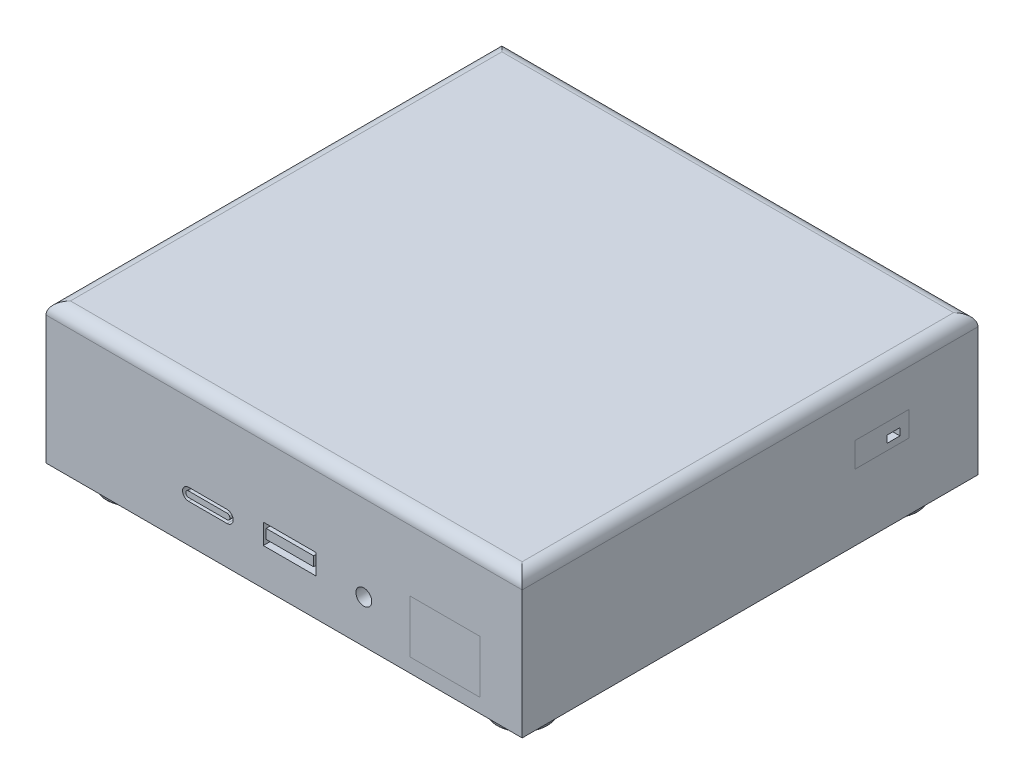
SolidWorks part; units mm, degrees
ref_plane "前视基准面" through (0, 0, 0) normal (0, 0, 1) x (1, 0, 0)
ref_plane "上视基准面" through (0, 0, 0) normal (0, 1, 0) x (1, 0, 0)
ref_plane "右视基准面" through (0, 0, 0) normal (1, 0, 0) x (0, 0, -1)
sketch "草图2" plane through (0, 0, 0) normal (0, 1, 0) x (1, 0, 0)
  line L1 (-58.5, -56) -> (58.5, -56)
  line L2 (-58.5, -56) -> (-58.5, 56)
  line L3 (-58.5, 56) -> (58.5, 56)
  line L4 (58.5, -56) -> (58.5, 56)
  line L5 (-58.5, -56) -> (58.5, 56) construction
  line L6 (-58.5, 56) -> (58.5, -56) construction
  point P0 (0, 0)
  dimension "D1" = 112
  dimension "D2" = 117
extrude "凸台-拉伸1" add sketch "草图2" along normal blind 34.5
fillet "圆角1" radius 3 4 edges at (0, 34.5, 56) (-58.5, 34.5, 0) (0, 34.5, -56) (58.5, 34.5, 0)
sketch "草图4" plane through (0, 0, 56) normal (0, 0, 1) x (1, 0, 0)
  line L1 (30.8918, 16.4329) -> (48.1943, 16.4329)
  line L2 (30.8918, 16.4329) -> (30.8918, 3.4592)
  line L3 (30.8918, 3.4592) -> (48.1943, 3.4592)
  line L4 (48.1943, 16.4329) -> (48.1943, 3.4592)
split line "分割线1"
sketch "草图5" plane through (0, 0, 56) normal (0, 0, 1) x (1, 0, 0)
  line L0 (-23.4533, 10.8763) -> (-14.0134, 10.8763) construction
  line L1 (-5.1124, 14.1395) -> (7.8876, 14.1395)
  line L2 (-5.1124, 14.1395) -> (-5.1124, 9.1395)
  line L3 (-5.1124, 9.1395) -> (7.8876, 9.1395)
  line L4 (7.8876, 14.1395) -> (7.8876, 9.1395)
  line L5 (-4.4095, 13.1395) -> (7.2461, 13.1395)
  line L6 (-4.4095, 13.1395) -> (-4.4095, 10.8025)
  line L7 (-4.4095, 10.8025) -> (7.2461, 10.8025)
  line L8 (7.2461, 13.1395) -> (7.2461, 10.8025)
  line L9 (-23.4533, 12.3763) -> (-14.0134, 12.3763)
  line L10 (-23.4533, 9.3763) -> (-14.0134, 9.3763)
  line L11 (-23.4533, 10.8763) -> (-14.0134, 10.8763) construction
  line L12 (-23.4533, 11.5763) -> (-14.0134, 11.5763)
  line L13 (-23.4533, 10.1763) -> (-14.0134, 10.1763)
  circle A0 centre (19.5946, 10.5373) radius 1.9432
  arc A1 (-23.4533, 12.3763) -> (-23.4533, 9.3763) centre (-23.4533, 10.8763) ccw
  arc A2 (-14.0134, 9.3763) -> (-14.0134, 12.3763) centre (-14.0134, 10.8763) ccw
  arc A3 (-23.4533, 11.5763) -> (-23.4533, 10.1763) centre (-23.4533, 10.8763) ccw
  arc A4 (-14.0134, 10.1763) -> (-14.0134, 11.5763) centre (-14.0134, 10.8763) ccw
  point P12 (-18.7333, 10.8763)
  point P17 (-18.7333, 10.8763)
  dimension "D1" = 13
  dimension "D2" = 5
  dimension "D3" = 1
  dimension "D4" = 0.703
  dimension "D5" = 1.4
  dimension "D6" = 3
extrude "切除-拉伸1" cut sketch "草图5" against normal blind 34.5
sketch "草图6" plane through (58.5, 0, 0) normal (1, 0, 0) x (0, 0, -1)
  line L1 (25.7543, 22.4016) -> (38.9963, 22.4016)
  line L2 (25.7543, 22.4016) -> (25.7543, 16.3039)
  line L3 (25.7543, 16.3039) -> (38.9963, 16.3039)
  line L4 (38.9963, 22.4016) -> (38.9963, 16.3039)
split line "分割线2"
sketch "草图7" plane through (58.5, 0, 0) normal (1, 0, 0) x (0, 0, -1)
  line L1 (33.6904, 19.6204) -> (36.8117, 19.6204)
  line L2 (33.6904, 19.6204) -> (33.6904, 17.871)
  line L3 (33.6904, 17.871) -> (36.8117, 17.871)
  line L4 (36.8117, 19.6204) -> (36.8117, 17.871)
extrude "切除-拉伸2" cut sketch "草图7" against normal blind 34.5
sketch "草图9" plane through (0, 0, -56) normal (0, 0, -1) x (-1, 0, 0)
  line L0 (-37.9278, 26.9668) -> (-37.9278, 21.2789)
  line L1 (-42.9278, 27.9668) -> (-41.2237, 27.9668)
  line L2 (-43.9278, 26.9668) -> (-43.9278, 21.2789)
  line L3 (-42.9278, 20.2789) -> (-41.2237, 20.2789)
  line L4 (-40.2237, 26.9668) -> (-40.2237, 21.2789)
  line L5 (-36.9278, 27.9668) -> (-35.2237, 27.9668)
  line L6 (-34.2237, 26.9668) -> (-34.2237, 21.2789)
  line L7 (-36.9278, 20.2789) -> (-35.2237, 20.2789)
  line L8 (-31.9278, 26.9668) -> (-31.9278, 21.2789)
  line L9 (-30.9278, 27.9668) -> (-29.2237, 27.9668)
  line L10 (-28.2237, 26.9668) -> (-28.2237, 21.2789)
  line L11 (-30.9278, 20.2789) -> (-29.2237, 20.2789)
  line L12 (-25.9278, 26.9668) -> (-25.9278, 21.2789)
  line L13 (-24.9278, 27.9668) -> (-23.2237, 27.9668)
  line L14 (-22.2237, 26.9668) -> (-22.2237, 21.2789)
  line L15 (-24.9278, 20.2789) -> (-23.2237, 20.2789)
  line L16 (-19.9278, 26.9668) -> (-19.9278, 21.2789)
  line L17 (-18.9278, 27.9668) -> (-17.2237, 27.9668)
  line L18 (-16.2237, 26.9668) -> (-16.2237, 21.2789)
  line L19 (-18.9278, 20.2789) -> (-17.2237, 20.2789)
  line L20 (-13.9278, 26.9668) -> (-13.9278, 21.2789)
  line L21 (-12.9278, 27.9668) -> (-11.2237, 27.9668)
  line L22 (-10.2237, 26.9668) -> (-10.2237, 21.2789)
  line L23 (-12.9278, 20.2789) -> (-11.2237, 20.2789)
  line L24 (-7.9278, 26.9668) -> (-7.9278, 21.2789)
  line L25 (-6.9278, 27.9668) -> (-5.2237, 27.9668)
  line L26 (-4.2237, 26.9668) -> (-4.2237, 21.2789)
  line L27 (-6.9278, 20.2789) -> (-5.2237, 20.2789)
  line L28 (-1.9278, 26.9668) -> (-1.9278, 21.2789)
  line L29 (-0.9278, 27.9668) -> (0.7763, 27.9668)
  line L30 (1.7763, 26.9668) -> (1.7763, 21.2789)
  line L31 (-0.9278, 20.2789) -> (0.7763, 20.2789)
  line L32 (4.0722, 26.9668) -> (4.0722, 21.2789)
  line L33 (5.0722, 27.9668) -> (6.7763, 27.9668)
  line L34 (7.7763, 26.9668) -> (7.7763, 21.2789)
  line L35 (5.0722, 20.2789) -> (6.7763, 20.2789)
  line L36 (10.0722, 26.9668) -> (10.0722, 21.2789)
  line L37 (11.0722, 27.9668) -> (12.7763, 27.9668)
  line L38 (13.7763, 26.9668) -> (13.7763, 21.2789)
  line L39 (11.0722, 20.2789) -> (12.7763, 20.2789)
  line L40 (16.0722, 26.9668) -> (16.0722, 21.2789)
  line L41 (17.0722, 27.9668) -> (18.7763, 27.9668)
  line L42 (19.7763, 26.9668) -> (19.7763, 21.2789)
  line L43 (17.0722, 20.2789) -> (18.7763, 20.2789)
  line L44 (22.0722, 26.9668) -> (22.0722, 21.2789)
  line L45 (23.0722, 27.9668) -> (24.7763, 27.9668)
  line L46 (25.7763, 26.9668) -> (25.7763, 21.2789)
  line L47 (23.0722, 20.2789) -> (24.7763, 20.2789)
  line L48 (28.0722, 26.9668) -> (28.0722, 21.2789)
  line L49 (29.0722, 27.9668) -> (30.7763, 27.9668)
  line L50 (31.7763, 26.9668) -> (31.7763, 21.2789)
  line L51 (29.0722, 20.2789) -> (30.7763, 20.2789)
  line L52 (34.0722, 26.9668) -> (34.0722, 21.2789)
  line L53 (35.0722, 27.9668) -> (36.7763, 27.9668)
  line L54 (37.7763, 26.9668) -> (37.7763, 21.2789)
  line L55 (35.0722, 20.2789) -> (36.7763, 20.2789)
  line L56 (-27.3597, 13.1324) -> (-19.9278, 13.1324)
  line L57 (-10.2237, 16.3161) -> (2.71, 16.3161)
  line L58 (-10.2237, 16.3161) -> (-10.2237, 8.6137)
  line L59 (-10.2237, 8.6137) -> (2.71, 8.6137)
  line L60 (2.71, 16.3161) -> (2.71, 8.6137)
  line L61 (-6.9278, 8.6137) -> (0.7763, 8.6137)
  line L62 (-6.9278, 8.6137) -> (-6.9278, 6.4855)
  line L63 (-6.9278, 6.4855) -> (0.7763, 6.4855)
  line L64 (0.7763, 8.6137) -> (0.7763, 6.4855)
  line L65 (11.0722, 16.3161) -> (21.5343, 16.3161)
  line L66 (11.0722, 16.3161) -> (11.0722, 11.0368)
  line L67 (11.0722, 11.0368) -> (21.5343, 11.0368)
  line L68 (21.5343, 16.3161) -> (21.5343, 11.0368)
  line L69 (11.0722, 8.6137) -> (21.5343, 8.6137)
  line L70 (11.0722, 8.6137) -> (11.0722, 3.4)
  line L71 (11.0722, 3.4) -> (21.5343, 3.4)
  line L72 (21.5343, 8.6137) -> (21.5343, 3.4)
  line L73 (12.7763, 15.5885) -> (19.7763, 15.5885)
  line L74 (12.7763, 15.5885) -> (12.7763, 13.6764)
  line L75 (12.7763, 13.6764) -> (19.7763, 13.6764)
  line L76 (19.7763, 15.5885) -> (19.7763, 13.6764)
  line L77 (12.7763, 7.5496) -> (19.7763, 7.5496)
  line L78 (12.7763, 7.5496) -> (12.7763, 6.0068)
  line L79 (12.7763, 6.0068) -> (19.7763, 6.0068)
  line L80 (19.7763, 7.5496) -> (19.7763, 6.0068)
  line L81 (-18.9278, 11.5446) -> (-18.9278, 8.6137)
  line L82 (-18.9278, 8.6137) -> (-35.9505, 8.6137)
  line L83 (-35.9505, 8.6137) -> (-35.9505, 11.5446)
  line L84 (-34.2237, 13.1324) -> (-27.3597, 13.1324)
  line L86 (31.3672, 15.5885) -> (38.4011, 15.5885) construction
  line L87 (-32.7426, 10.4251) -> (-20.7193, 10.4251)
  line L88 (-32.7426, 10.4251) -> (-32.7426, 9.7224)
  line L89 (-32.7426, 9.7224) -> (-20.7193, 9.7224)
  line L90 (-20.7193, 10.4251) -> (-20.7193, 9.7224)
  line L91 (31.3672, 17.3412) -> (38.4011, 17.3412)
  line L92 (31.3672, 13.8358) -> (38.4011, 13.8358)
  line L93 (31.3672, 15.5885) -> (38.4011, 15.5885) construction
  line L94 (31.3672, 15.9777) -> (38.4011, 15.9777)
  line L95 (31.3672, 15.1993) -> (38.4011, 15.1993)
  arc A0 (-40.2237, 26.9668) -> (-41.2237, 27.9668) centre (-41.2237, 26.9668) ccw
  arc A1 (-41.2237, 20.2789) -> (-40.2237, 21.2789) centre (-41.2237, 21.2789) ccw
  arc A2 (-43.9278, 21.2789) -> (-42.9278, 20.2789) centre (-42.9278, 21.2789) ccw
  arc A3 (-43.9278, 26.9668) -> (-42.9278, 27.9668) centre (-42.9278, 26.9668) cw
  arc A4 (-37.9278, 26.9668) -> (-36.9278, 27.9668) centre (-36.9278, 26.9668) cw
  arc A5 (-37.9278, 21.2789) -> (-36.9278, 20.2789) centre (-36.9278, 21.2789) ccw
  arc A6 (-34.2237, 26.9668) -> (-35.2237, 27.9668) centre (-35.2237, 26.9668) ccw
  arc A7 (-35.2237, 20.2789) -> (-34.2237, 21.2789) centre (-35.2237, 21.2789) ccw
  arc A8 (-31.9278, 26.9668) -> (-30.9278, 27.9668) centre (-30.9278, 26.9668) cw
  arc A9 (-31.9278, 21.2789) -> (-30.9278, 20.2789) centre (-30.9278, 21.2789) ccw
  arc A10 (-28.2237, 26.9668) -> (-29.2237, 27.9668) centre (-29.2237, 26.9668) ccw
  arc A11 (-29.2237, 20.2789) -> (-28.2237, 21.2789) centre (-29.2237, 21.2789) ccw
  arc A12 (-25.9278, 26.9668) -> (-24.9278, 27.9668) centre (-24.9278, 26.9668) cw
  arc A13 (-25.9278, 21.2789) -> (-24.9278, 20.2789) centre (-24.9278, 21.2789) ccw
  arc A14 (-22.2237, 26.9668) -> (-23.2237, 27.9668) centre (-23.2237, 26.9668) ccw
  arc A15 (-23.2237, 20.2789) -> (-22.2237, 21.2789) centre (-23.2237, 21.2789) ccw
  arc A16 (-19.9278, 26.9668) -> (-18.9278, 27.9668) centre (-18.9278, 26.9668) cw
  arc A17 (-19.9278, 21.2789) -> (-18.9278, 20.2789) centre (-18.9278, 21.2789) ccw
  arc A18 (-16.2237, 26.9668) -> (-17.2237, 27.9668) centre (-17.2237, 26.9668) ccw
  arc A19 (-17.2237, 20.2789) -> (-16.2237, 21.2789) centre (-17.2237, 21.2789) ccw
  arc A20 (-13.9278, 26.9668) -> (-12.9278, 27.9668) centre (-12.9278, 26.9668) cw
  arc A21 (-13.9278, 21.2789) -> (-12.9278, 20.2789) centre (-12.9278, 21.2789) ccw
  arc A22 (-10.2237, 26.9668) -> (-11.2237, 27.9668) centre (-11.2237, 26.9668) ccw
  arc A23 (-11.2237, 20.2789) -> (-10.2237, 21.2789) centre (-11.2237, 21.2789) ccw
  arc A24 (-7.9278, 26.9668) -> (-6.9278, 27.9668) centre (-6.9278, 26.9668) cw
  arc A25 (-7.9278, 21.2789) -> (-6.9278, 20.2789) centre (-6.9278, 21.2789) ccw
  arc A26 (-4.2237, 26.9668) -> (-5.2237, 27.9668) centre (-5.2237, 26.9668) ccw
  arc A27 (-5.2237, 20.2789) -> (-4.2237, 21.2789) centre (-5.2237, 21.2789) ccw
  arc A28 (-1.9278, 26.9668) -> (-0.9278, 27.9668) centre (-0.9278, 26.9668) cw
  arc A29 (-1.9278, 21.2789) -> (-0.9278, 20.2789) centre (-0.9278, 21.2789) ccw
  arc A30 (1.7763, 26.9668) -> (0.7763, 27.9668) centre (0.7763, 26.9668) ccw
  arc A31 (0.7763, 20.2789) -> (1.7763, 21.2789) centre (0.7763, 21.2789) ccw
  arc A32 (4.0722, 26.9668) -> (5.0722, 27.9668) centre (5.0722, 26.9668) cw
  arc A33 (4.0722, 21.2789) -> (5.0722, 20.2789) centre (5.0722, 21.2789) ccw
  arc A34 (7.7763, 26.9668) -> (6.7763, 27.9668) centre (6.7763, 26.9668) ccw
  arc A35 (6.7763, 20.2789) -> (7.7763, 21.2789) centre (6.7763, 21.2789) ccw
  arc A36 (10.0722, 26.9668) -> (11.0722, 27.9668) centre (11.0722, 26.9668) cw
  arc A37 (10.0722, 21.2789) -> (11.0722, 20.2789) centre (11.0722, 21.2789) ccw
  arc A38 (13.7763, 26.9668) -> (12.7763, 27.9668) centre (12.7763, 26.9668) ccw
  arc A39 (12.7763, 20.2789) -> (13.7763, 21.2789) centre (12.7763, 21.2789) ccw
  arc A40 (16.0722, 26.9668) -> (17.0722, 27.9668) centre (17.0722, 26.9668) cw
  arc A41 (16.0722, 21.2789) -> (17.0722, 20.2789) centre (17.0722, 21.2789) ccw
  arc A42 (19.7763, 26.9668) -> (18.7763, 27.9668) centre (18.7763, 26.9668) ccw
  arc A43 (18.7763, 20.2789) -> (19.7763, 21.2789) centre (18.7763, 21.2789) ccw
  arc A44 (22.0722, 26.9668) -> (23.0722, 27.9668) centre (23.0722, 26.9668) cw
  arc A45 (22.0722, 21.2789) -> (23.0722, 20.2789) centre (23.0722, 21.2789) ccw
  arc A46 (25.7763, 26.9668) -> (24.7763, 27.9668) centre (24.7763, 26.9668) ccw
  arc A47 (24.7763, 20.2789) -> (25.7763, 21.2789) centre (24.7763, 21.2789) ccw
  arc A48 (28.0722, 26.9668) -> (29.0722, 27.9668) centre (29.0722, 26.9668) cw
  arc A49 (28.0722, 21.2789) -> (29.0722, 20.2789) centre (29.0722, 21.2789) ccw
  arc A50 (31.7763, 26.9668) -> (30.7763, 27.9668) centre (30.7763, 26.9668) ccw
  arc A51 (30.7763, 20.2789) -> (31.7763, 21.2789) centre (30.7763, 21.2789) ccw
  arc A52 (34.0722, 26.9668) -> (35.0722, 27.9668) centre (35.0722, 26.9668) cw
  arc A53 (34.0722, 21.2789) -> (35.0722, 20.2789) centre (35.0722, 21.2789) ccw
  arc A54 (37.7763, 26.9668) -> (36.7763, 27.9668) centre (36.7763, 26.9668) ccw
  arc A55 (36.7763, 20.2789) -> (37.7763, 21.2789) centre (36.7763, 21.2789) ccw
  arc A56 (-19.9278, 13.1324) -> (-18.9278, 11.5446) centre (-18.1673, 13.1324) ccw
  arc A57 (-35.9505, 11.5446) -> (-34.2237, 13.1324) centre (-35.9505, 13.2775) ccw
  circle A58 centre (-47.9425, 10.4251) radius 3.1055
  circle A59 centre (-47.9425, 10.4251) radius 1.2689
  arc A60 (31.3672, 17.3412) -> (31.3672, 13.8358) centre (31.3672, 15.5885) ccw
  arc A61 (38.4011, 13.8358) -> (38.4011, 17.3412) centre (38.4011, 15.5885) ccw
  arc A62 (31.3672, 15.9777) -> (31.3672, 15.1993) centre (31.3672, 15.5885) ccw
  arc A63 (38.4011, 15.1993) -> (38.4011, 15.9777) centre (38.4011, 15.5885) ccw
  point P210 (34.8841, 15.5885)
  point P215 (34.8841, 15.5885)
  dimension "D1" = 1
  dimension "D3" = 2.2958
  dimension "D2" = 14
extrude "切除-拉伸3" cut sketch "草图9" against normal blind 34.5 contours A57 L83 L82 L81 A56 L56 L84 L87 L90 L89 L88 | A58 A59 | L60 L57 L58 L59 | L64 L59 L62 L63 | L68 L65 L66 L67 L73 L76 L75 L74 | L72 L69 L70 L71 L77 L80 L79 L78 | L92 A61 L91 A60 A63 L95 A62 L94 | L55 A55 L54 A54 L53 A52 L52 A53 | L51 A51 L50 A50 L49 A48 L48 A49 | L47 A47 L46 A46 L45 A44 L44 A45 | L43 A43 L42 A42 L41 A40 L40 A41 | L39 A39 L38 A38 L37 A36 L36 A37 | L35 A35 L34 A34 L33 A32 L32 A33 | L31 A31 L30 A30 L29 A28 L28 A29 | L27 A27 L26 A26 L25 A24 L24 A25 | L23 A23 L22 A22 L21 A20 L20 A21 | L19 A19 L18 A18 L17 A16 L16 A17 | L15 A15 L14 A14 L13 A12 L12 A13 | L11 A11 L10 A10 L9 A8 L8 A9 | L7 A7 L6 A6 L5 A4 L0 A5 | A3 L2 A2 L3 A1 L4 A0 L1
sketch "草图10" plane through (-58.5, 0, 0) normal (-1, 0, 0) x (0, 0, 1)
  line L1 (5.1153, 18.3972) -> (42.7001, 18.3972)
  line L2 (5.1153, 18.3972) -> (5.1153, 11.8393)
  line L3 (5.1153, 11.8393) -> (42.7001, 11.8393)
  line L4 (42.7001, 18.3972) -> (42.7001, 11.8393)
split line "分割线3"
sketch "草图11" plane through (-58.5, 0, 0) normal (-1, 0, 0) x (0, 0, 1)
  line L1 (14.0865, 16.0909) -> (40.5013, 16.0909)
  line L2 (14.0865, 16.0909) -> (14.0865, 14.5913)
  line L3 (14.0865, 14.5913) -> (40.5013, 14.5913)
  line L4 (40.5013, 16.0909) -> (40.5013, 14.5913)
extrude "切除-拉伸4" cut sketch "草图11" against normal blind 34.5
sketch "草图12" plane through (-58.5, 0, 0) normal (-1, 0, 0) x (0, 0, 1)
  line L0 (6.9233, 16.2269) -> (8.9907, 16.2269)
  line L1 (8.9907, 16.2269) -> (10.5166, 14.701)
  line L2 (10.5166, 14.701) -> (10.5166, 12.2516)
  line L3 (10.5166, 12.2516) -> (6.9233, 12.2516)
  line L4 (6.9233, 12.2516) -> (6.9233, 16.2269)
  text T0 "SD"
split line "分割线4"
sketch "草图13" plane through (0, 0, 0) normal (0, -1, 0) x (1, 0, 0)
  line L0 (48, 0) -> (58.5, 0) construction
  line L1 (48, 45.5) -> (-48, 45.5) construction
  line L2 (48, 45.5) -> (48, -45.5) construction
  line L3 (48, -45.5) -> (-48, -45.5) construction
  line L4 (-48, 45.5) -> (-48, -45.5) construction
  line L5 (58.5, 56) -> (58.5, -56) construction
  line L6 (-48, 0) -> (-58.5, 0) construction
  line L7 (-58.5, -56) -> (-58.5, 56) construction
  line L10 (-58.5, 56) -> (58.5, 56) construction
  line L11 (0, 56) -> (0, 45.5) construction
  line L13 (0, -45.5) -> (0, -56) construction
  line L14 (58.5, -56) -> (-58.5, -56) construction
  circle A0 centre (48, 45.5) radius 6.25
  circle A1 centre (48, -45.5) radius 6.25
  circle A2 centre (-48, 45.5) radius 6.25
  circle A3 centre (-48, -45.5) radius 6.25
  dimension "D2" = 12.5
  dimension "D1" = 91
extrude "凸台-拉伸2" add sketch "草图13" along normal blind 5
sketch "草图14" plane through (0, -5, 0) normal (0, -1, 0) x (1, 0, 0)
  circle A0 centre (48, 45.5) radius 4
  circle A1 centre (48, -45.5) radius 4
  circle A2 centre (-48, 45.5) radius 4
  circle A3 centre (-48, -45.5) radius 4
  circle A4 centre (48, 45.5) radius 6.25 construction
  circle A5 centre (48, -45.5) radius 6.25 construction
  circle A6 centre (-48, 45.5) radius 6.25 construction
  circle A7 centre (-48, -45.5) radius 6.25 construction
  dimension "D1" = 8
extrude "切除-拉伸5" cut sketch "草图14" against normal blind 5
sketch "草图15" plane through (0, 0, 0) normal (0, -1, 0) x (1, 0, 0)
  line L0 (0, 56) -> (0, -56) construction
  line L1 (-58.5, 56) -> (58.5, 56) construction
  line L2 (58.5, -56) -> (-58.5, -56) construction
  line L3 (0, 0) -> (37.1628, 0) construction
  circle A0 centre (0, 42.5) radius 1.5
  circle A1 centre (0, -42.5) radius 1.5
  dimension "D1" = 85
  dimension "D2" = 3
extrude "切除-拉伸6" cut sketch "草图15" against normal blind 5
sketch "草图16" plane through (0, 0, 0) normal (0, -1, 0) x (1, 0, 0)
  line L0 (48, -30.5) -> (48, 30.5)
  line L1 (3.3404, -37.3051) -> (-4.3833, -37.3051)
  line L2 (33, 45.5) -> (11.9716, 45.5)
  line L3 (-4.3833, -37.3051) -> (-11.9716, -45.5)
  line L4 (-48, 30.5) -> (-48, -30.5)
  line L5 (23.7102, 0) -> (0, 0) construction
  line L6 (-33, -45.5) -> (-11.9716, -45.5)
  line L7 (0, 0) -> (0, -15.7999) construction
  line L8 (-3.3404, -37.3051) -> (4.3833, -37.3051)
  line L9 (4.3833, -37.3051) -> (11.9716, -45.5)
  line L10 (-3.3404, 37.3051) -> (4.3833, 37.3051)
  line L11 (4.3833, 37.3051) -> (11.9716, 45.5)
  line L12 (3.3404, 37.3051) -> (-4.3833, 37.3051)
  line L13 (-4.3833, 37.3051) -> (-11.9716, 45.5)
  line L14 (11.9716, -45.5) -> (33, -45.5)
  line L15 (-11.9716, 45.5) -> (-33, 45.5)
  arc A0 (33, 45.5) -> (48, 30.5) centre (48, 45.5) ccw
  arc A1 (48, -30.5) -> (33, -45.5) centre (48, -45.5) ccw
  arc A2 (-33, -45.5) -> (-48, -30.5) centre (-48, -45.5) ccw
  arc A3 (-48, 30.5) -> (-33, 45.5) centre (-48, 45.5) ccw
  dimension "D1" = 30
extrude "切除-拉伸7" cut sketch "草图16" against normal blind 1 contours A3 L4 A2 L6 L3 L1 L8 L9 L14 A1 L0 A0 L2 L11 L10 L12 L13 L15
fillet "圆角2" radius 3 16 edges at (-48, 0.5, -30.5) (-33, 0.5, -45.5) (-11.9716, 0.5, -45.5) (-4.3833, 0.5, -37.3051) (4.3833, 0.5, -37.3051) (11.9716, 0.5, -45.5) (33, 0.5, -45.5) (48, 0.5, -30.5) (48, 0.5, 30.5) (33, 0.5, 45.5) (4.3833, 0.5, 37.3051) (-4.3833, 0.5, 37.3051) (-11.9716, 0.5, 45.5) (-33, 0.5, 45.5) (-48, 0.5, 30.5) (11.9716, 0.5, 45.5)
fillet "圆角3" radius 0.5 8 edges at (-48, -5, 39.25) (-48, -5, 41.5) (-48, -5, -51.75) (-48, -5, -49.5) (48, -5, -51.75) (48, -5, -49.5) (48, -5, 39.25) (48, -5, 41.5)
sketch "草图17" plane through (0, 0, 0) normal (0, -1, 0) x (1, 0, 0)
  circle A0 centre (48, 45.5) radius 1.25
  circle A1 centre (48, 45.5) radius 4 construction
  circle A2 centre (48, -45.5) radius 1.25
  circle A3 centre (48, -45.5) radius 4 construction
  circle A4 centre (-48, 45.5) radius 1.25
  circle A5 centre (-48, 45.5) radius 4 construction
  circle A6 centre (-48, -45.5) radius 1.25
  circle A7 centre (-48, -45.5) radius 4 construction
  dimension "D1" = 2.5
extrude "切除-拉伸8" cut sketch "草图17" against normal blind 10
